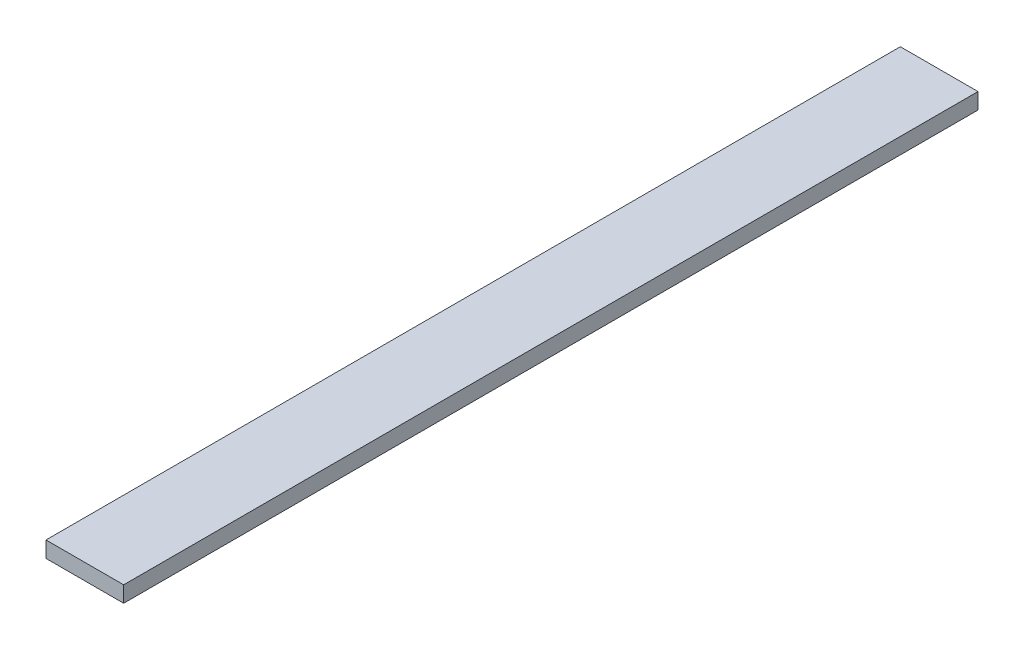
SolidWorks part; units mm, degrees
ref_plane "Front Plane" through (0, 0, 0) normal (0, 0, 1) x (1, 0, 0)
ref_plane "Top Plane" through (0, 0, 0) normal (0, 1, 0) x (1, 0, 0)
ref_plane "Right Plane" through (0, 0, 0) normal (1, 0, 0) x (0, 0, -1)
sketch "Sketch1" plane through (0, 0, 0) normal (0, 1, 0) x (1, 0, 0)
  line L1 (0, 0) -> (23.0909, 0)
  line L2 (0, 0) -> (0, -254)
  line L3 (0, -254) -> (23.0909, -254)
  line L4 (23.0909, 0) -> (23.0909, -254)
  dimension "D1" = 254
extrude "Boss-Extrude1" add sketch "Sketch1" along normal blind 4.7625 contours L1 L4 L3 L2
